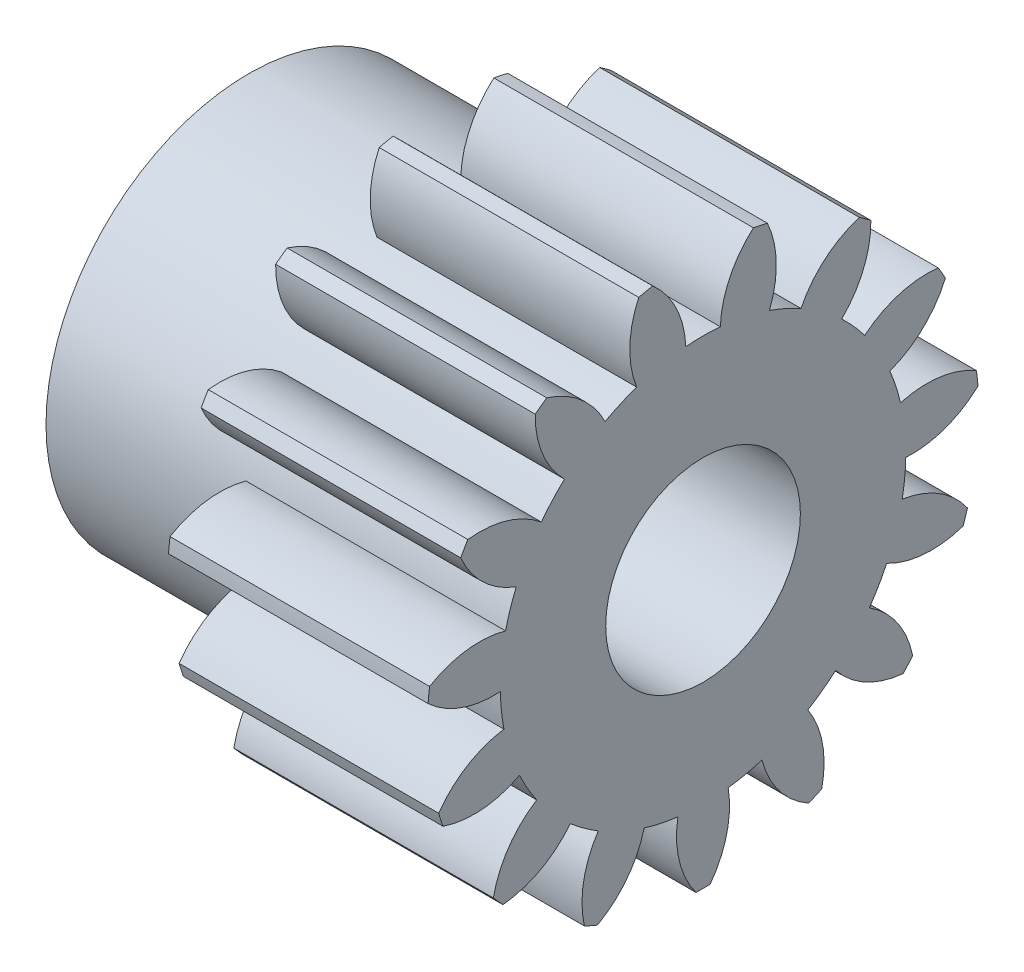
SolidWorks part; units mm, degrees
ref_plane "Plane1" through (0, 0, 0) normal (0, 0, 1) x (1, 0, 0)
ref_plane "Plane2" through (0, 0, 0) normal (0, 1, 0) x (1, 0, 0)
ref_plane "Plane3" through (0, 0, 0) normal (1, 0, 0) x (0, 0, -1)
sketch "HoldingSke" plane through (0, 0, 0) normal (0, 1, 0) x (1, 0, 0)
  line L0 (0, 0) -> (0.9659, -0.2588)
  line L1 (-15, 0) -> (100, 0) construction
  line L2 (0, 0) -> (-2.1039, 2.3779)
  line L3 (0, 0) -> (-11.863, 4.5341)
  line L4 (0, 0) -> (8.3417, 2.2352)
  line L5 (0, 0) -> (-10.3065, -3.844)
  line L6 (0, 0) -> (-6.6317, -4.4744)
  line L7 (-2.1039, 2.3779) -> (0.2639, 13.1202)
  line L8 (-76.2, 54.61) -> (-75.2, 54.61)
  line L9 (-71.009, 38.7566) -> (-53.1078, 45.2721)
  line L10 (-76.2, 71.12) -> (104.1128, 71.12)
  line L11 (0, 0) -> (-8, 0)
  line L12 (-76.2, 101.6) -> (-76.162, 101.6)
  line L13 (24.9733, 27.94) -> (52.9518, 28.4284)
  line L14 (24.9733, 27.94) -> (24.9743, 27.94)
  line L15 (24.9733, 27.94) -> (100.4006, 29.5858)
  line L16 (-63.627, -1) -> (-12.827, -1)
  circle A0 centre (0, 0) radius 3
  circle A1 centre (0, 0) radius 6.249
  circle A2 centre (0, 0) radius 6.5
  circle A3 centre (0, 0) radius 3
  dimension "MHD" = 12.498
  dimension "Hub_dia" = 13
  dimension "Bore" = 6
  dimension "MBD" = 6
  dimension "Num_teeth" = 15
  dimension "Pitch" = 1
  dimension "Overall_len" = 11
  dimension "Show_teeth" = 15
  dimension "Thickness" = 8
  dimension "OAL" = 11.0002
  dimension "T_dim" = 1
  dimension "Ap" = 20
  dimension "H" = 19.05
  dimension "Pitch_radius" = 180.3128
  dimension "Width" = 8
  dimension "Backlash" = 0.038
  dimension "Addendum_fac" = 1
  dimension "Dedendum_fac" = 1.25
  dimension "Clearance_fac" = 0.25
  dimension "Dedendum_add" = 0.001
  dimension "Module" = 1
sketch "BasProSke" plane through (0, 0, 0) normal (0, 1, 0) x (1, 0, 0)
  line L0 (-10, 0) -> (60, 0) construction
  line L1 (0, 0) -> (0, 8.5)
  line L2 (0, 0) -> (8, 0)
  line L3 (8, 0) -> (8, 8.5)
  line L4 (8, 8.5) -> (0, 8.5)
  dimension "Thickness" = 8
  dimension "Diameter" = 17
revolve "Base-Revolve" add sketch "BasProSke" angle 360 about L0
sketch "TooCutSke" plane through (0, 0, 0) normal (1, 0, 0) x (0, 0, -1)
  line L1 (0, 0) -> (0, 107) construction
  line L2 (0, 0) -> (-0.8504, 7.4516) construction
  line L3 (0, 0) -> (-3.1044, 14.6049) construction
  line L4 (-0.8504, 7.4516) -> (-1.5522, 7.3025) construction
  arc A0 (0.5316, 6.2263) -> (-0.5316, 6.2263) centre (0, 0) ccw
  arc A1 (1.5766, 8.3784) -> (-1.5766, 8.3784) centre (0, 0) ccw
  circle A2 centre (0, 0) radius 7.5 construction
  circle A3 centre (0, 0) radius 7.0477 construction
  arc A4 (-0.5316, 6.2263) -> (-1.5766, 8.3784) centre (-3.5289, 6.1005) ccw
  arc A5 (1.5766, 8.3784) -> (0.5316, 6.2263) centre (3.5289, 6.1005) ccw
  dimension "Root_dia" = 12.498
  dimension "Overcut_dia" = 17.0508
  dimension "Pitch_dia" = 15
  dimension "Base_dia" = 14.0954
  dimension "Flank_rad" = 3
  dimension "Half_ang" = 12
  dimension "Half_CT" = 0.7175
extrude "ToothCut" cut sketch "TooCutSke" along normal through all
fillet "Breaks" [suppressed] radius 0.02
fillet "RootFillets" [suppressed] radius 0.251
pattern_circular "TeethCuts" count 15 every 24 about axis through (-10, 0, 0) along (1, 0, 0) of "ToothCut", "RootFillets", "Breaks"
sketch "HubNeaOneSke" plane through (0, 0, 0) normal (-1, 0, 0) x (0, 0, 1)
  circle A0 centre (0, 0) radius 6.249
  dimension "Diameter" = 12.498
extrude "HubNearOne" add sketch "HubNeaOneSke" along normal blind 3.0002
ref_plane "FarPln" through (8, 0, 0) normal (1, 0, 0) x (0, 0, -1)
sketch "BorSke" plane through (0, 0, 0) normal (1, 0, 0) x (0, 0, -1)
  circle A0 centre (0, 0) radius 3
  dimension "Diameter" = 6
extrude "Bore" cut sketch "BorSke" along normal mid plane 22.0003
other "Move Face1" face at (-3.0002, 0, 3) parameters "D1"=3
equation "' \"Module@HoldingSke\" = 6.35"
equation "' \"Num_teeth@HoldingSke\" = 12"
equation "' \"Ap@HoldingSke\" =  20"
equation "' \"Ap@HoldingSke\" = 20"
equation "' \"Width@HoldingSke\" = 0.5 * 25.4"
equation "' \"Hub_dia@HoldingSke\"= 1 * 25.4"
equation "' \"Hub_dia@HoldingSke\" = 1 * 25.4"
equation "' \"Overall_len@HoldingSke\" = 1.0 * 25.4"
equation "' \"Bore@HoldingSke\" = 0.75 * 25.4"
equation "' \"T_dim@HoldingSke\" = 0.1 * 25.4"
equation "' \"Width@KeySke\" = 0.25 * 25.4"
equation "' \"Show_teeth@HoldingSke\" = 13"
equation "' \"Backlash@HoldingSke\" = 0.009 * 25.4"
equation "' \"Addendum_fac@HoldingSke\" = 1.0"
equation "' \"Dedendum_fac@HoldingSke\" = 1.25"
equation "' \"Dedendum_add@HoldingSke\" = 0.00005 * 25.4"
equation "' \"Clearance_fac@HoldingSke\" = 0.25"
equation "\"Pitch@HoldingSke\" = 1 / \"Module@HoldingSke\""
equation "\"Overcut_dia@TooCutSke\" = (\"Num_teeth@HoldingSke\" + 2 * \"Addendum_fac@HoldingSke\") / \"Pitch@HoldingSke\" + 0.002 * 25.4"
equation "\"Pitch_dia@TooCutSke\" = \"Num_teeth@HoldingSke\" / \"Pitch@HoldingSke\""
equation "\"Base_dia@TooCutSke\" = \"Num_teeth@HoldingSke\" / \"Pitch@HoldingSke\" * cos((\"Ap@HoldingSke\"  * 3.14159265 / 180))"
equation "\"Root_dia@TooCutSke\" = (\"Num_teeth@HoldingSke\" + 2) / \"Pitch@HoldingSke\" - 2 * (\"Addendum_fac@HoldingSke\" + \"Dedendum_fac@HoldingSke\") / \"Pitch@HoldingSke\" - \"Dedendum_add@HoldingSke\" * 2"
equation "\"Half_ang@TooCutSke\" = 180 / \"Num_teeth@HoldingSke\""
equation "\"Half_CT@TooCutSke\" = \"Num_teeth@HoldingSke\" / \"Pitch@HoldingSke\" * sin((3.14159265 / 2 / \"Num_teeth@HoldingSke\")) / 2 - 7 * \"Backlash@HoldingSke\" / 4"
equation "\"Flank_rad@TooCutSke\" = \"Num_teeth@HoldingSke\" / \"Pitch@HoldingSke\" / 5"
equation "\"Radius@RootFillets\" = \"Clearance_fac@HoldingSke\" / \"Pitch@HoldingSke\" + \"Dedendum_add@HoldingSke\""
equation "\"Break_rad@Breaks\" = 0.02 / \"Pitch@HoldingSke\""
equation "\"Thickness@HoldingSke\" = \"Width@HoldingSke\""
equation "\"OAL@HoldingSke\" = \"Thickness@HoldingSke\""
equation "\"MHD@HoldingSke\" = (\"Num_teeth@HoldingSke\" + 2) / \"Pitch@HoldingSke\" - 2 * (\"Addendum_fac@HoldingSke\" + \"Dedendum_fac@HoldingSke\")  / \"Pitch@HoldingSke\" - \"Dedendum_add@HoldingSke\" * 2"
equation "\"MBD@HoldingSke\" = (\"Num_teeth@HoldingSke\" + 2) / \"Pitch@HoldingSke\" - 2 * (\"Addendum_fac@HoldingSke\" + \"Dedendum_fac@HoldingSke\")  / \"Pitch@HoldingSke\" - \"Dedendum_add@HoldingSke\" * 2 - 0.002 * 25.4"
equation "\"MHD@HoldingSke\" = ((sgn( \"MHD@HoldingSke\" - \"Hub_dia@HoldingSke\" )-1)*( \"MHD@HoldingSke\" - \"Hub_dia@HoldingSke\" ))/-2+ \"Hub_dia@HoldingSke\""
equation "\"MBD@HoldingSke\" = ((sgn( \"MBD@HoldingSke\" - \"Bore@HoldingSke\" )-1)*( \"MBD@HoldingSke\" - \"Bore@HoldingSke\" ))/-2+ \"Bore@HoldingSke\""
equation "\"OAL@HoldingSke\" = ((sgn( \"OAL@HoldingSke\" - \"Overall_len@HoldingSke\" )+1)*( \"OAL@HoldingSke\" - \"Overall_len@HoldingSke\" ))/2 + \"Overall_len@HoldingSke\" + 0.000002 * 25.4"
equation "\"Num_teeth@TeethCuts\" = int( \"Show_teeth@HoldingSke\" ) + 1"
equation "\"Num_teeth@TeethCuts\" = ((sgn( \"Num_teeth@TeethCuts\" - \"Num_teeth@HoldingSke\" )-1)*( \"Num_teeth@TeethCuts\" - \"Num_teeth@HoldingSke\" ))/-2+ \"Num_teeth@HoldingSke\""
equation "\"Num_teeth@TeethCuts\" = ((sgn( \"Num_teeth@TeethCuts\" - 2.0)+1)*( \"Num_teeth@TeethCuts\" - 2.0))/2 +2.0"
equation "\"Angle@TeethCuts\" = 360.0 / \"Num_teeth@HoldingSke\""
equation "\"Diameter@BasProSke\" = (\"Num_teeth@HoldingSke\" + 2 * \"Addendum_fac@HoldingSke\") / \"Pitch@HoldingSke\""
equation "\"Thickness@BasProSke\"  = \"Thickness@HoldingSke\""
equation "' \"Fillet_rad@BasProSke\" =  \"Thickness@HoldingSke\" * 0.05"
equation "' \"Fillet_rad@BasProSke\" = \"Thickness@HoldingSke\" * 0.05"
equation "\"MHD@HoldingSke\" = ((sgn( \"MHD@HoldingSke\" - \"Root_dia@TooCutSke\" )-1)*( \"MHD@HoldingSke\" - \"Root_dia@TooCutSke\" ))/-2+ \"Root_dia@TooCutSke\""
equation "\"Diameter@HubNeaOneSke\" = \"MHD@HoldingSke\""
equation "\"Length@HubNearOne\" = \"OAL@HoldingSke\" - \"Thickness@BasProSke\""
equation "\"Thickness@FarPln\" = \"Thickness@BasProSke\""
equation "\"Diameter@BorSke\" = \"MBD@HoldingSke\""
equation "\"D1@Bore\" = \"OAL@HoldingSke\" * 2.0"
